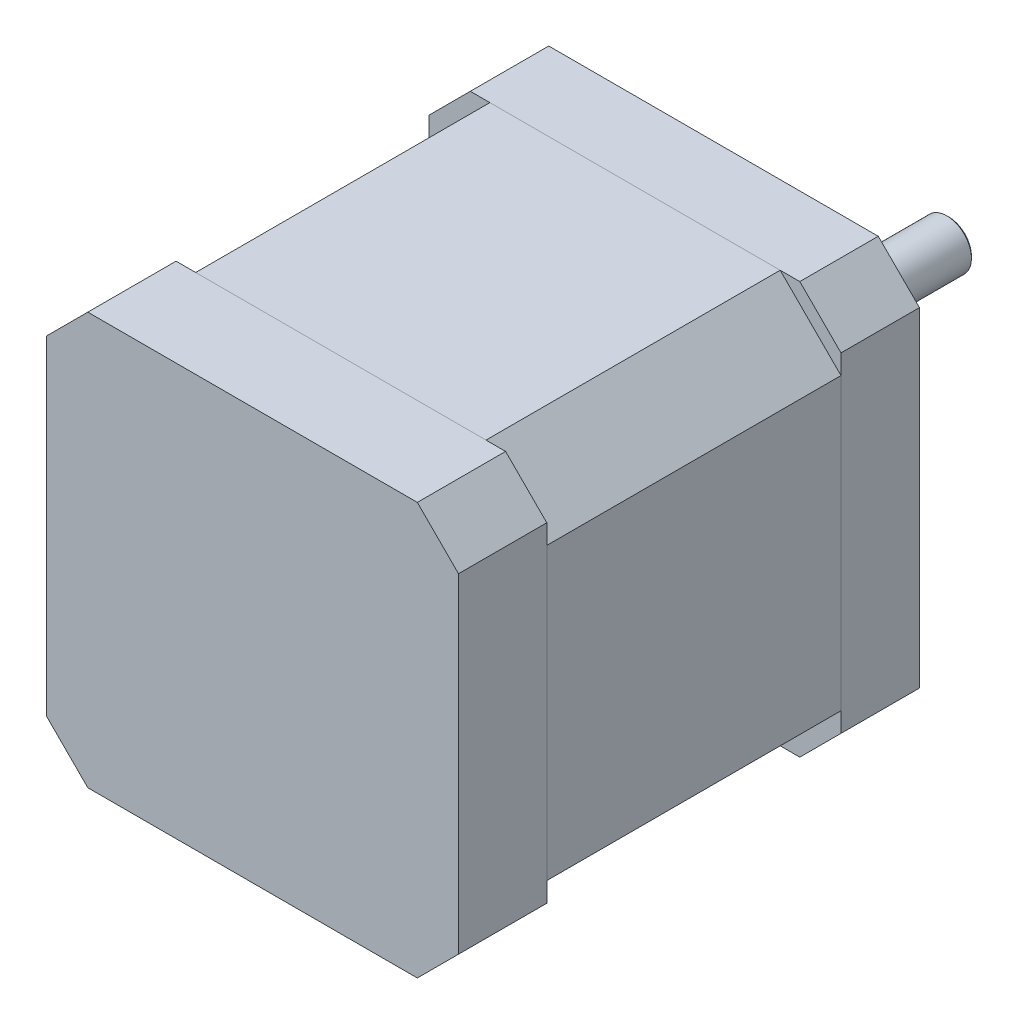
SolidWorks part; units mm, degrees
ref_plane "Plan de face" through (0, 0, 0) normal (0, 0, 1) x (1, 0, 0)
ref_plane "Plan de dessus" through (0, 0, 0) normal (0, 1, 0) x (1, 0, 0)
ref_plane "Plan de droite" through (0, 0, 0) normal (1, 0, 0) x (0, 0, -1)
sketch "Esquisse1" plane through (0, 0, 0) normal (0, 0, 1) x (1, 0, 0)
  line L1 (-21, 21) -> (21, 21)
  line L2 (-21, 21) -> (-21, -21)
  line L3 (-21, -21) -> (21, -21)
  line L4 (21, 21) -> (21, -21)
  line L5 (-21, 21) -> (21, -21) construction
  line L6 (-21, -21) -> (21, 21) construction
  point P0 (0, 0)
  dimension "D1" = 42
  dimension "D2" = 42
extrude "Boss.-Extru.1" add sketch "Esquisse1" along normal blind 8
chamfer "Chanfrein1" distance 4.2 angle 45 4 edges at (-21, -21, 4) (-21, 21, 4) (21, 21, 4) (21, -21, 4)
sketch "Esquisse3" plane through (0, 0, 8) normal (0, 0, 1) x (1, 0, 0)
  line L0 (-21, 14.8) -> (-14.8, 21)
  line L1 (-14.8, 21) -> (14.8, 21)
  line L2 (-21, 14.8) -> (-21, -14.8)
  line L3 (-14.8, -21) -> (14.8, -21)
  line L4 (21, 14.8) -> (21, -14.8)
  line L5 (-21, 21) -> (21, -21) construction
  line L6 (-21, -21) -> (21, 21) construction
  line L7 (14.8, 21) -> (21, 14.8)
  line L8 (14.8, -21) -> (21, -14.8)
  line L9 (-21, -14.8) -> (-14.8, -21)
  point P0 (0, 0)
  dimension "D1" = 42
  dimension "D2" = 42
extrude "Boss.-Extru.2" add sketch "Esquisse3" along normal blind 30 separate body
sketch "Esquisse4" plane through (0, 0, 38) normal (0, 0, 1) x (1, 0, 0)
  line L1 (-21, -21) -> (21, -21)
  line L2 (-21, -21) -> (-21, 21)
  line L3 (-21, 21) -> (21, 21)
  line L4 (21, -21) -> (21, 21)
  line L5 (-21, -21) -> (21, 21) construction
  line L6 (-21, 21) -> (21, -21) construction
  point P0 (0, 0)
  dimension "D1" = 42
  dimension "D2" = 42
extrude "Boss.-Extru.3" add sketch "Esquisse4" along normal blind 9 separate body
chamfer "Chanfrein3" distance 4.2 angle 45 4 edges at (21, 21, 42.5) (21, -21, 42.5) (-21, -21, 42.5) (-21, 21, 42.5)
sketch "Esquisse5" plane through (0, 0, 0) normal (0, 0, -1) x (-1, 0, 0)
  circle A0 centre (0, 0) radius 11
  dimension "D1" = 22
extrude "Boss.-Extru.4" add sketch "Esquisse5" along normal blind 2
sketch "Esquisse6" plane through (0, 0, -2) normal (0, 0, -1) x (-1, 0, 0)
  circle A0 centre (0, 0) radius 4.5
  dimension "D1" = 9
extrude "Enlèv. mat.-Extru.1" cut sketch "Esquisse6" against normal blind 3
sketch "Esquisse7" plane through (0, 0, 1) normal (0, 0, -1) x (-1, 0, 0)
  circle A0 centre (0, 0) radius 2.5
  dimension "D1" = 5
extrude "Boss.-Extru.5" add sketch "Esquisse7" along normal blind 25
chamfer "Chanfrein4" distance 0.2 angle 45 1 edges at (-2.5, 0, -24)
sketch "Esquisse8" plane through (0, 0, 0) normal (0, 0, -1) x (-1, 0, 0)
  line L1 (-15.5, 15.5) -> (15.5, 15.5) construction
  line L2 (-15.5, 15.5) -> (-15.5, -15.5) construction
  line L3 (-15.5, -15.5) -> (15.5, -15.5) construction
  line L4 (15.5, 15.5) -> (15.5, -15.5) construction
  line L5 (-15.5, 15.5) -> (15.5, -15.5) construction
  line L6 (-15.5, -15.5) -> (15.5, 15.5) construction
  circle A0 centre (-15.5, 15.5) radius 1.5
  circle A1 centre (15.5, 15.5) radius 1.5
  circle A2 centre (15.5, -15.5) radius 1.5
  circle A3 centre (-15.5, -15.5) radius 1.5
  point P0 (0, 0)
  dimension "D3" = 3
  dimension "D1" = 31
  dimension "D2" = 31
extrude "Enlèv. mat.-Extru.2" cut sketch "Esquisse8" against normal blind 5
chamfer "Chanfrein5" distance 0.2 angle 45 4 edges at (14, -15.5, 0) (-17, -15.5, 0) (-17, 15.5, 0) (14, 15.5, 0)
sketch "Esquisse9" plane through (-21, 0, 0) normal (-1, 0, 0) x (0, 0, 1)
  line L0 (41.5, 0) -> (38, 0) construction
  line L1 (38, -4) -> (45, -4)
  line L2 (38, -4) -> (38, 4)
  line L3 (38, 4) -> (45, 4)
  line L4 (45, -4) -> (45, 4)
  line L5 (38, -4) -> (45, 4) construction
  line L6 (38, 4) -> (45, -4) construction
  line L7 (38, 16.8) -> (38, -16.8) construction
  point P0 (41.5, 0)
  dimension "D1" = 7
  dimension "D2" = 8
extrude "Enlèv. mat.-Extru.3" cut sketch "Esquisse9" against normal blind 2
